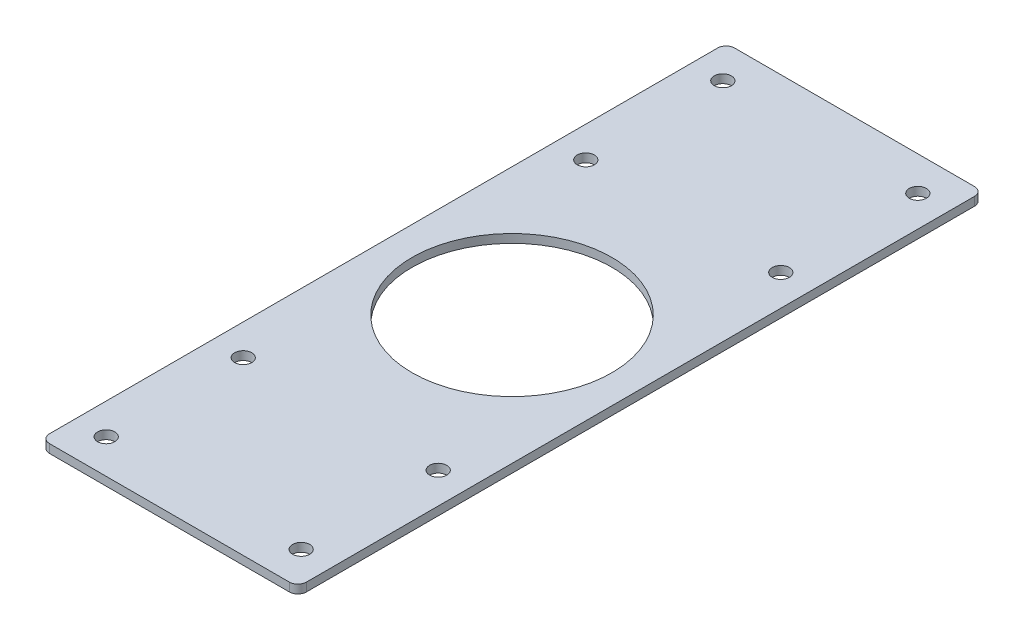
SolidWorks part; units mm, degrees
material "AISI 1045 Steel, cold drawn"
ref_plane "Front Plane" through (0, 0, 0) normal (0, 0, 1) x (1, 0, 0)
ref_plane "Top Plane" through (0, 0, 0) normal (0, 1, 0) x (1, 0, 0)
ref_plane "Right Plane" through (0, 0, 0) normal (1, 0, 0) x (0, 0, -1)
sketch "Sketch1" plane through (0, 0, 0) normal (0, 1, 0) x (1, 0, 0)
  line L0 (0, 0) -> (0, 120) construction
  line L1 (-45, -120) -> (45, -120)
  line L2 (-45, -120) -> (-45, 120)
  line L3 (-45, 120) -> (45, 120)
  line L4 (45, -120) -> (45, 120)
  line L5 (-45, -120) -> (45, 120) construction
  line L6 (-45, 120) -> (45, -120) construction
  line L7 (0, 0) -> (45, 0) construction
  line L8 (-34.15, 60) -> (-34.15, 108) construction
  circle A0 centre (0, 0) radius 35
  circle A1 centre (-34.15, 60) radius 3
  circle A2 centre (34.15, 60) radius 3
  circle A3 centre (34.15, -60) radius 3
  circle A4 centre (-34.15, -60) radius 3
  circle A5 centre (-34.15, 108) radius 3
  circle A6 centre (34.15, 108) radius 3
  circle A7 centre (-34.15, -108) radius 3
  circle A8 centre (34.15, -108) radius 3
  point P0 (0, 0)
  dimension "D3" = 6
  dimension "D4" = 34.15
  dimension "D5" = 60
  dimension "D6" = 70
  dimension "D1" = 90
  dimension "D2" = 240
  dimension "D8" = 48
  dimension "D7" = 2
  dimension "D9" = 2
extrude "Boss-Extrude1" add sketch "Sketch1" along normal blind 3
fillet "Fillet1" radius 3 4 edges at (-45, 1.5, -120) (45, 1.5, -120) (-45, 1.5, 120) (45, 1.5, 120)
